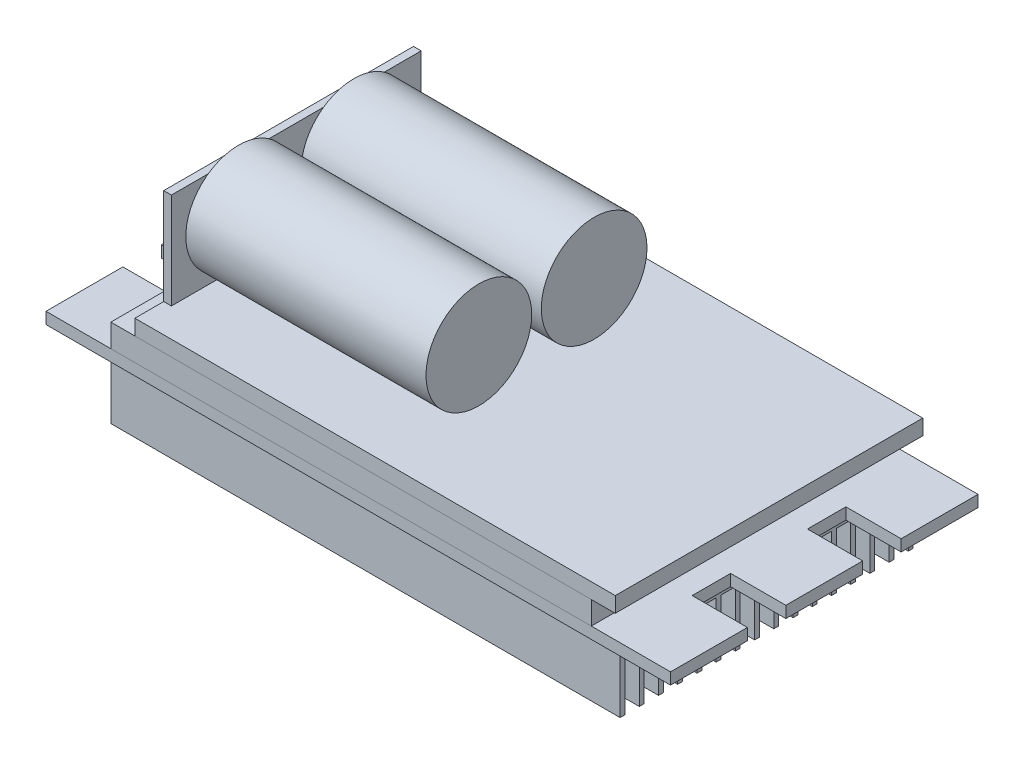
SolidWorks part; units mm, degrees
material "Copper"
ref_plane "Front Plane" through (0, 0, 0) normal (0, 0, 1) x (1, 0, 0)
ref_plane "Top Plane" through (0, 0, 0) normal (0, 1, 0) x (1, 0, 0)
ref_plane "Right Plane" through (0, 0, 0) normal (1, 0, 0) x (0, 0, -1)
sketch "Sketch1" plane through (0, 0, 0) normal (0, 1, 0) x (1, 0, 0)
  line L0 (-26.75, 16) -> (-32.5, 16)
  line L1 (-26.75, -16) -> (26.75, -16)
  line L2 (-26.75, -16) -> (-26.75, 16) construction
  line L3 (-26.75, 16) -> (26.75, 16)
  line L4 (26.75, -16) -> (26.75, 16) construction
  line L5 (-26.75, -16) -> (26.75, 16) construction
  line L6 (-26.75, 16) -> (26.75, -16) construction
  line L7 (-32.5, 16) -> (-32.5, 8)
  line L8 (-32.5, 8) -> (-26.75, 8)
  line L9 (-26.75, 4) -> (-32.5, 4)
  line L10 (-32.5, 4) -> (-32.5, -4)
  line L11 (-32.5, -4) -> (-26.75, -4)
  line L12 (-26.75, -16) -> (-32.5, -16)
  line L13 (-32.5, -16) -> (-32.5, -8)
  line L14 (-32.5, -8) -> (-26.75, -8)
  line L15 (0, 0) -> (-32.5, 0) construction
  line L16 (26.75, 16) -> (32.5, 16)
  line L17 (32.5, 16) -> (32.5, 8)
  line L18 (32.5, 8) -> (26.75, 8)
  line L19 (26.75, -16) -> (32.5, -16)
  line L20 (32.5, -16) -> (32.5, -8)
  line L21 (32.5, -8) -> (26.75, -8)
  line L22 (26.75, 4) -> (32.5, 4)
  line L23 (32.5, 4) -> (32.5, -4)
  line L24 (32.5, -4) -> (26.75, -4)
  line L25 (0, 0) -> (32.5, 0) construction
  line L26 (-26.75, 8) -> (-26.75, 4)
  line L27 (-26.75, -4) -> (-26.75, -8)
  line L28 (26.75, 8) -> (26.75, 4)
  line L29 (26.75, -4) -> (26.75, -8)
  point P0 (0, 0)
  dimension "D1" = 53.5
  dimension "D2" = 32
  dimension "D3" = 65
  dimension "D4" = 8
extrude "Boss-Extrude1" add sketch "Sketch1" along normal blind 1.2
sketch "Sketch2" plane through (0, 1.2, 0) normal (0, 1, 0) x (1, 0, 0)
  line L0 (32.5, 16) -> (-32.5, 16) construction
  line L1 (-25.75, -16) -> (24.25, -16)
  line L2 (-25.75, -16) -> (-25.75, 16)
  line L3 (-25.75, 16) -> (24.25, 16)
  line L4 (24.25, -16) -> (24.25, 16)
  line L5 (-25.75, -16) -> (24.25, 16) construction
  line L6 (-25.75, 16) -> (24.25, -16) construction
  line L7 (-26.75, 8) -> (-26.75, 4) construction
  point P0 (-0.75, 0)
  dimension "D1" = 50
  dimension "D2" = 1
extrude "Boss-Extrude2" add sketch "Sketch2" along normal blind 2.4 separate body
sketch "Sketch3" plane through (0, 3.6, 0) normal (0, 1, 0) x (1, 0, 0)
  line L0 (32.5, 16) -> (-32.5, 16) construction
  line L1 (26.75, -16) -> (-23.25, -16)
  line L2 (26.75, -16) -> (26.75, 16)
  line L3 (26.75, 16) -> (-23.25, 16)
  line L4 (-23.25, -16) -> (-23.25, 16)
  line L5 (26.75, -16) -> (-23.25, 16) construction
  line L6 (26.75, 16) -> (-23.25, -16) construction
  line L7 (26.75, 4) -> (26.75, 8) construction
  point P0 (1.75, 0)
  dimension "D1" = 50
extrude "Boss-Extrude3" add sketch "Sketch3" along normal blind 1.6 separate body
sketch "Sketch4" plane through (0, 5.2, 0) normal (0, 1, 0) x (1, 0, 0)
  line L1 (-23.25, -13) -> (-22.45, -13)
  line L2 (-23.25, -13) -> (-23.25, 13)
  line L3 (-23.25, 13) -> (-22.45, 13)
  line L4 (-22.45, -13) -> (-22.45, 13)
  line L5 (-23.25, -13) -> (-22.45, 13) construction
  line L6 (-23.25, 13) -> (-22.45, -13) construction
  line L8 (-23.25, 16) -> (-23.25, -16) construction
  point P0 (-22.85, 0)
  point P5 (0, 0)
  point P9 (0, 0)
  dimension "D1" = 0.8
  dimension "D2" = 26
extrude "Boss-Extrude4" add sketch "Sketch4" along normal blind 10
sketch "Sketch5" plane through (-22.45, 0, 0) normal (1, 0, 0) x (0, 0, -1)
  line L0 (-16, 5.2) -> (16, 5.2) construction
  line L1 (6, 10.7) -> (-6, 10.7) construction
  line L2 (6, 10.7) -> (6, 5.2) construction
  line L3 (6, 5.2) -> (-6, 5.2) construction
  line L4 (-6, 10.7) -> (-6, 5.2) construction
  line L5 (6, 10.7) -> (-6, 5.2) construction
  line L6 (6, 5.2) -> (-6, 10.7) construction
  circle A0 centre (-6, 10.7) radius 5.5
  circle A1 centre (6, 10.7) radius 5.5
  point P0 (0, 7.95)
  dimension "D3" = 11
  dimension "D1" = 5.5
  dimension "D2" = 12
extrude "Boss-Extrude6" add sketch "Sketch5" along normal blind 25 separate body
sketch "Sketch6" plane through (0, 0, 0) normal (0, -1, 0) x (-1, 0, 0)
  line L5 (26.5, 15.25) -> (-26.5, 15.25)
  line L6 (26.5, 15.25) -> (26.5, -15.25)
  line L7 (26.5, -15.25) -> (-26.5, -15.25)
  line L8 (-26.5, 15.25) -> (-26.5, -15.25)
  line L9 (26.5, 15.25) -> (-26.5, -15.25) construction
  line L10 (26.5, -15.25) -> (-26.5, 15.25) construction
  point P0 (0, 0)
  point P1 (0, 0)
  dimension "D1" = 53
  dimension "D2" = 30.5
extrude "Boss-Extrude7" add sketch "Sketch6" along normal blind 6.3
sketch "Sketch8" plane through (26.5, 0, 0) normal (1, 0, 0) x (0, 0, -1)
  line L0 (-15.25, 0) -> (-15.25, -6.3)
  line L1 (-15.25, -6.3) -> (-14.75, -6.3)
  line L2 (15.25, -6.3) -> (-15.25, -6.3) construction
  line L3 (-14.75, -6.3) -> (-14.75, -0.5)
  line L5 (15.25, 0) -> (15.25, -6.3)
  line L6 (15.25, -6.3) -> (14.75, -6.3)
  line L8 (-15.25, 0) -> (-23.6125, 0)
  line L9 (-23.6125, 0) -> (-23.6125, -15.9473)
  line L10 (-23.6125, -15.9473) -> (23.6125, -15.9473)
  line L11 (23.6125, -15.9473) -> (23.6125, 0)
  line L12 (23.6125, 0) -> (15.25, 0)
  line L13 (-14.75, -0.5) -> (-13.25, -0.5)
  line L14 (-13.25, -0.5) -> (-13.25, -6.3)
  line L15 (-13.25, -6.3) -> (-12.75, -6.3)
  line L16 (-12.75, -6.3) -> (-12.75, -0.5)
  line L18 (-12.75, -0.5) -> (-11.25, -0.5)
  line L19 (-11.25, -0.5) -> (-11.25, -6.3)
  line L20 (-11.25, -6.3) -> (-10.75, -6.3)
  line L21 (-10.75, -6.3) -> (-10.75, -0.5)
  line L22 (-10.75, -0.5) -> (-9.25, -0.5)
  line L23 (-9.25, -0.5) -> (-9.25, -6.3)
  line L24 (-9.25, -6.3) -> (-8.75, -6.3)
  line L25 (-8.75, -6.3) -> (-8.75, -0.5)
  line L26 (-8.75, -0.5) -> (-7.25, -0.5)
  line L27 (-7.25, -0.5) -> (-7.25, -6.3)
  line L28 (-7.25, -6.3) -> (-6.75, -6.3)
  line L29 (-6.75, -6.3) -> (-6.75, -0.5)
  line L30 (-6.75, -0.5) -> (-5.25, -0.5)
  line L31 (-5.25, -0.5) -> (-5.25, -6.3)
  line L32 (-5.25, -6.3) -> (-4.75, -6.3)
  line L33 (-4.75, -6.3) -> (-4.75, -0.5)
  line L34 (-4.75, -0.5) -> (-3.25, -0.5)
  line L35 (-3.25, -0.5) -> (-3.25, -6.3)
  line L36 (-3.25, -6.3) -> (-2.75, -6.3)
  line L37 (-2.75, -6.3) -> (-2.75, -0.5)
  line L38 (-2.75, -0.5) -> (-1.25, -0.5)
  line L39 (-1.25, -0.5) -> (-1.25, -6.3)
  line L40 (-1.25, -6.3) -> (-0.75, -6.3)
  line L41 (-0.75, -6.3) -> (-0.75, -0.5)
  line L42 (-0.75, -0.5) -> (0.75, -0.5)
  line L43 (0.75, -0.5) -> (0.75, -6.3)
  line L44 (0.75, -6.3) -> (1.25, -6.3)
  line L45 (1.25, -6.3) -> (1.25, -0.5)
  line L46 (1.25, -0.5) -> (2.75, -0.5)
  line L47 (2.75, -0.5) -> (2.75, -6.3)
  line L48 (2.75, -6.3) -> (3.25, -6.3)
  line L49 (3.25, -6.3) -> (3.25, -0.5)
  line L50 (3.25, -0.5) -> (4.75, -0.5)
  line L51 (4.75, -0.5) -> (4.75, -6.3)
  line L52 (4.75, -6.3) -> (5.25, -6.3)
  line L53 (5.25, -6.3) -> (5.25, -0.5)
  line L54 (5.25, -0.5) -> (6.75, -0.5)
  line L55 (6.75, -0.5) -> (6.75, -6.3)
  line L56 (6.75, -6.3) -> (7.25, -6.3)
  line L57 (7.25, -6.3) -> (7.25, -0.5)
  line L58 (7.25, -0.5) -> (8.75, -0.5)
  line L59 (8.75, -0.5) -> (8.75, -6.3)
  line L60 (8.75, -6.3) -> (9.25, -6.3)
  line L61 (9.25, -6.3) -> (9.25, -0.5)
  line L62 (9.25, -0.5) -> (10.75, -0.5)
  line L63 (10.75, -0.5) -> (10.75, -6.3)
  line L64 (10.75, -6.3) -> (11.25, -6.3)
  line L65 (11.25, -6.3) -> (11.25, -0.5)
  line L66 (11.25, -0.5) -> (12.75, -0.5)
  line L67 (12.75, -0.5) -> (12.75, -6.3)
  line L68 (12.75, -6.3) -> (13.25, -6.3)
  line L69 (13.25, -6.3) -> (13.25, -0.5)
  line L70 (13.25, -0.5) -> (14.75, -0.5)
  line L71 (14.75, -0.5) -> (14.75, -6.3)
  line L72 (14.75, -6.3) -> (15.25, -6.3)
  line L73 (15.25, -6.3) -> (15.25, -0.5)
  point P13 (0, 0)
  line M7 (-15.25, 0) -> (-15.25, -6.3)
  line M8 (-15.25, -6.3) -> (15.25, -6.3)
  line M9 (15.25, -6.3) -> (15.25, 0)
  dimension "D1" = 0.5
  dimension "D2" = 5.8
  dimension "D3" = 2
  dimension "D4" = 0.5
  dimension "D5" = 15
extrude "Cut-Extrude7" cut sketch "Sketch8" against normal through all contours L11 L12 L5 L8 L9 L10 M9 M8 M7 | L14 L13 L3 M8 | L19 L18 L16 M8 | L23 L22 L21 M8 | L27 L26 L25 M8 | L31 L30 L29 M8 | L35 L34 L33 M8 | L39 L38 L37 M8 | L43 L42 L41 M8 | L47 L46 L45 M8 | L51 L50 L49 M8 | L55 L54 L53 M8 | L59 L58 L57 M8 | L63 L62 L61 M8 | L67 L66 L65 M8 | L71 L70 L69 M8
